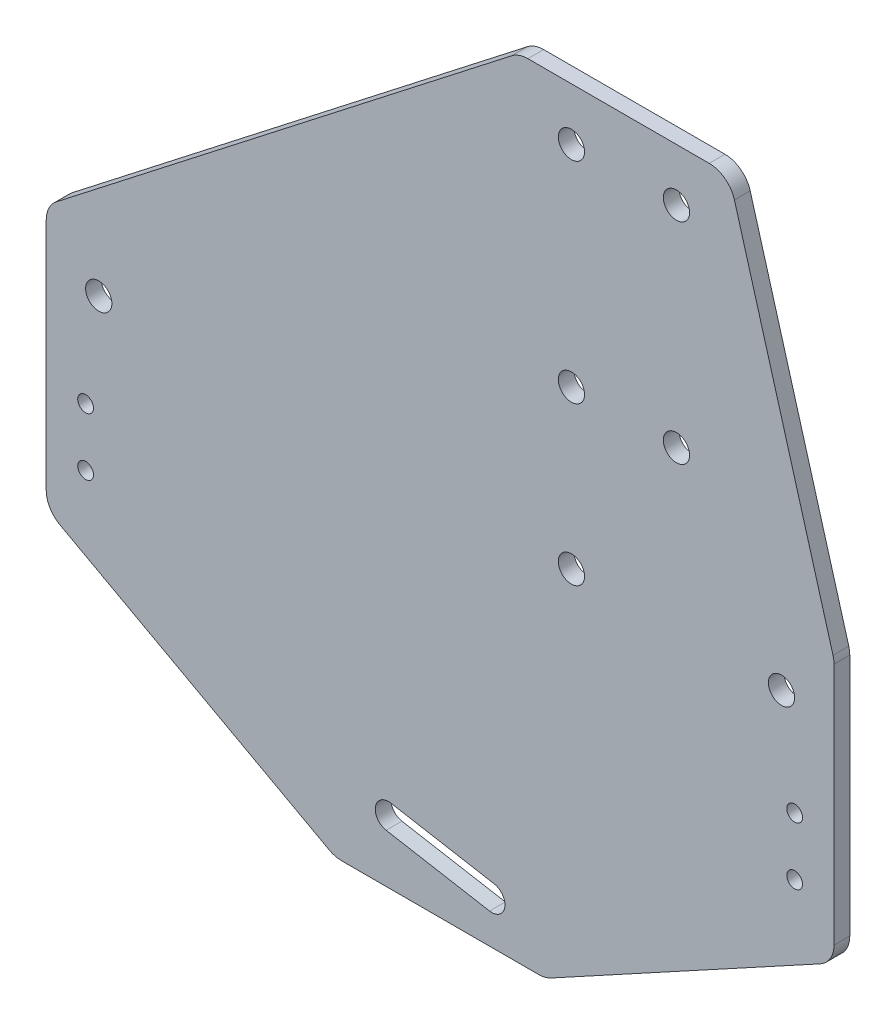
SolidWorks part; units mm, degrees
ref_plane "Front Plane" through (0, 0, 0) normal (0, 0, 1) x (1, 0, 0)
ref_plane "Top Plane" through (0, 0, 0) normal (0, 1, 0) x (1, 0, 0)
ref_plane "Right Plane" through (0, 0, 0) normal (1, 0, 0) x (0, 0, -1)
sketch "Sketch1" plane through (0, 0, 0) normal (0, 0, 1) x (1, 0, 0)
  line L0 (-75, 0) -> (-75, 80)
  line L1 (75, 0) -> (75, 80)
  line L2 (-75, 80) -> (15, 150)
  line L3 (-75, 0) -> (75, 0)
  line L4 (75, 80) -> (55, 150)
  line L5 (15, 150) -> (55, 150)
  point P4 (0, 0)
  dimension "D1" = 150
  dimension "D2" = 40
  dimension "D3" = 80
  dimension "D4" = 150
  dimension "D5" = 20
extrude "Boss-Extrude1" add sketch "Sketch1" along normal blind 3
sketch "Sketch2" plane through (0, 0, 3) normal (0, 0, 1) x (1, 0, 0)
  line L0 (-75, 0) -> (75, 0) construction
  line L1 (-9.8481, 11.7365) -> (9.8481, 8.2635) construction
  line L2 (75, 0) -> (75, 80) construction
  line L3 (0, 0) -> (0, 150) construction
  line L4 (-9.414, 14.1985) -> (10.2822, 10.7255)
  line L5 (-75, 80) -> (-75, 0) construction
  line L6 (-10.2822, 9.2745) -> (9.414, 5.8015)
  line L7 (-75, 0) -> (75, 0) construction
  circle A0 centre (-65, 70) radius 2.5
  arc A1 (-9.414, 14.1985) -> (-10.2822, 9.2745) centre (-9.8481, 11.7365) ccw
  arc A2 (9.414, 5.8015) -> (10.2822, 10.7255) centre (9.8481, 8.2635) ccw
  circle A3 centre (65, 70) radius 2.5
  circle A4 centre (67.5, 51) radius 1.5
  circle A5 centre (25, 70) radius 2.5
  circle A6 centre (67.5, 40) radius 1.5
  circle A7 centre (-67.5, 51) radius 1.5
  circle A8 centre (-67.5, 40) radius 1.5
  point P12 (0, 10)
  dimension "D1" = 5
  dimension "D2" = 70
  dimension "D3" = 10
  dimension "D4" = 40
  dimension "D5" = 2.5
  dimension "D9" = 3
  dimension "D10" = 7.5
  dimension "D11" = 11
  dimension "D12" = 40
  dimension "D6" = 10
  dimension "D7" = 10
  dimension "D8" = 20
extrude "Cut-Extrude1" cut sketch "Sketch2" against normal through all
sketch "Sketch3" plane through (0, 0, 3) normal (0, 0, 1) x (1, 0, 0)
  line L0 (55, 150) -> (15, 150) construction
  circle A0 centre (45, 140) radius 2.5
  dimension "D1" = 10
  dimension "D2" = 5
  dimension "D3" = 10
extrude "Cut-Extrude2" cut sketch "Sketch3" against normal through all
pattern_linear "LPattern1" count 2 spacing 20 along (-1, 0, 0) count 2 spacing 40 along (0, -1, 0) of "Cut-Extrude2"
sketch "Sketch4" plane through (0, 0, 3) normal (0, 0, 1) x (1, 0, 0)
  line L0 (-75, 30) -> (-20, 0)
  line L1 (-75, 80) -> (-75, 0) construction
  line L2 (-75, 0) -> (75, 0) construction
  line L3 (-20, 0) -> (-75, 0)
  line L4 (-75, 0) -> (-75, 30)
  line L5 (20, 0) -> (75, 30)
  line L6 (75, 0) -> (75, 80) construction
  line L7 (75, 30) -> (75, 0)
  line L8 (75, 0) -> (20, 0)
  dimension "D1" = 50
  dimension "D2" = 50
  dimension "D3" = 20
  dimension "D4" = 20
extrude "Cut-Extrude3" cut sketch "Sketch4" against normal through all
fillet "Fillet1" radius 5 8 edges at (-20, 0, 1.5) (20, 0, 1.5) (75, 30, 1.5) (75, 80, 1.5) (55, 150, 1.5) (15, 150, 1.5) (-75, 30, 1.5) (-75, 80, 1.5)
